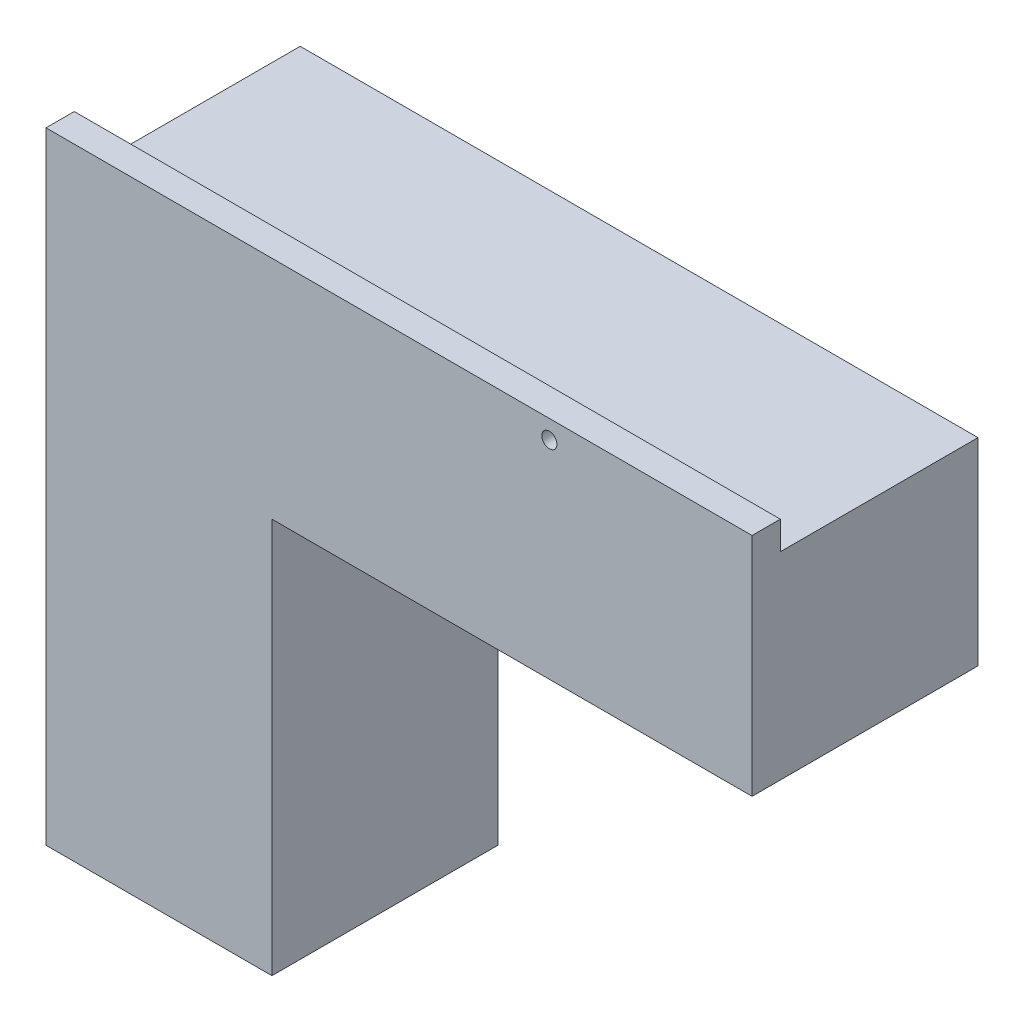
SolidWorks part; units mm, degrees
ref_plane "Спереди" through (0, 0, 0) normal (0, 0, 1) x (1, 0, 0)
ref_plane "Сверху" through (0, 0, 0) normal (0, 1, 0) x (1, 0, 0)
ref_plane "Справа" through (0, 0, 0) normal (1, 0, 0) x (0, 0, -1)
sketch "Эскиз1" plane through (0, 0, 0) normal (0, 0, 1) x (1, 0, 0)
  line L0 (0, 0) -> (0, 220)
  line L1 (0, 220) -> (250, 220)
  line L2 (250, 220) -> (250, 140)
  line L3 (250, 140) -> (80, 140)
  line L4 (80, 140) -> (80, 0)
  line L5 (80, 0) -> (0, 0)
extrude "Бобышка-Вытянуть1" add sketch "Эскиз1" along normal blind 80
sketch "Эскиз2" plane through (0, 0, 0) normal (0, -1, 0) x (1, 0, 0)
  line L1 (0, 0) -> (10, 0)
  line L2 (0, 0) -> (0, 70)
  line L3 (0, 70) -> (10, 70)
  line L4 (10, 0) -> (10, 70)
extrude "Вырез-Вытянуть1" cut sketch "Эскиз2" against normal blind 250
sketch "Эскиз3" plane through (250, 0, 0) normal (1, 0, 0) x (0, 0, -1)
  line L1 (0, 220) -> (-70, 220)
  line L2 (0, 220) -> (0, 210)
  line L3 (0, 210) -> (-70, 210)
  line L4 (-70, 220) -> (-70, 210)
extrude "Вырез-Вытянуть2" cut sketch "Эскиз3" against normal blind 250
sketch "Эскиз4" plane through (0, 0, 80) normal (0, 0, 1) x (1, 0, 0)
  circle A0 centre (178.2214, 213.3836) radius 2.6927
  point P2 (178.2214, 213.3836)
extrude "Вырез-Вытянуть3" cut sketch "Эскиз4" against normal blind 10
